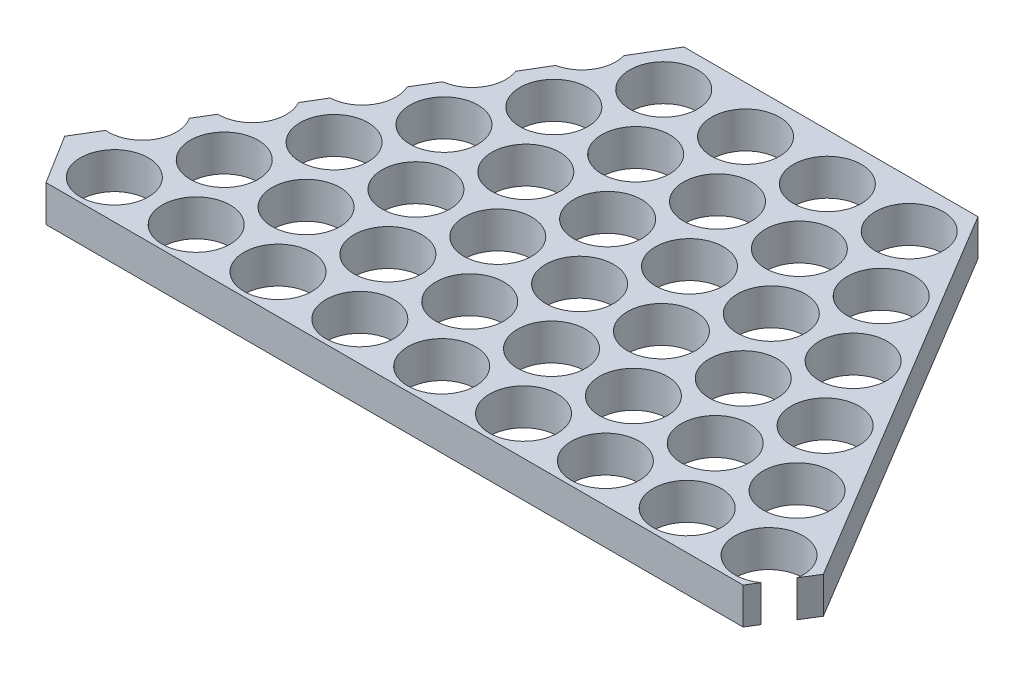
SolidWorks part; units mm, degrees
material "AISI 1020"
ref_plane "Front" through (0, 0, 0) normal (0, 0, 1) x (1, 0, 0)
ref_plane "Top" through (0, 0, 0) normal (0, 1, 0) x (1, 0, 0)
ref_plane "Right" through (0, 0, 0) normal (1, 0, 0) x (0, 0, -1)
sketch "Sketch1" plane through (0, 0, 0) normal (0, 1, 0) x (1, 0, 0)
  line L0 (8.3115, 12) -> (-7.8585, 12)
  line L1 (21.0855, -9.2779) -> (8.3115, 12)
  line L2 (19.3924, -12) -> (21.0855, -9.2779)
  line L3 (-18.9394, -12) -> (19.3924, -12)
  line L4 (-20.6326, -9.2779) -> (-18.9394, -12)
  line L5 (-7.8585, 12) -> (-20.6326, -9.2779)
extrude "Boss-Extrude1" add sketch "Sketch1" along normal blind 2
sketch "Sketch2" plane through (0, 2, 0) normal (0, 1, 0) x (1, 0, 0)
  circle A0 centre (7.1085, 9.4205) radius 1.868
extrude "Cut-Extrude1" cut sketch "Sketch2" against normal blind 2
pattern_linear "LPattern1" count 4 spacing 4.5 along (-1, 0, 0) of "Cut-Extrude1"
pattern_linear "LPattern2" count 6 spacing 4.5 along (0.5147, 0, 0.8574) of "Cut-Extrude1"
pattern_linear "LPattern3" count 9 spacing 4.5 along (-1, 0, 0) of "LPattern2", "Cut-Extrude1"
